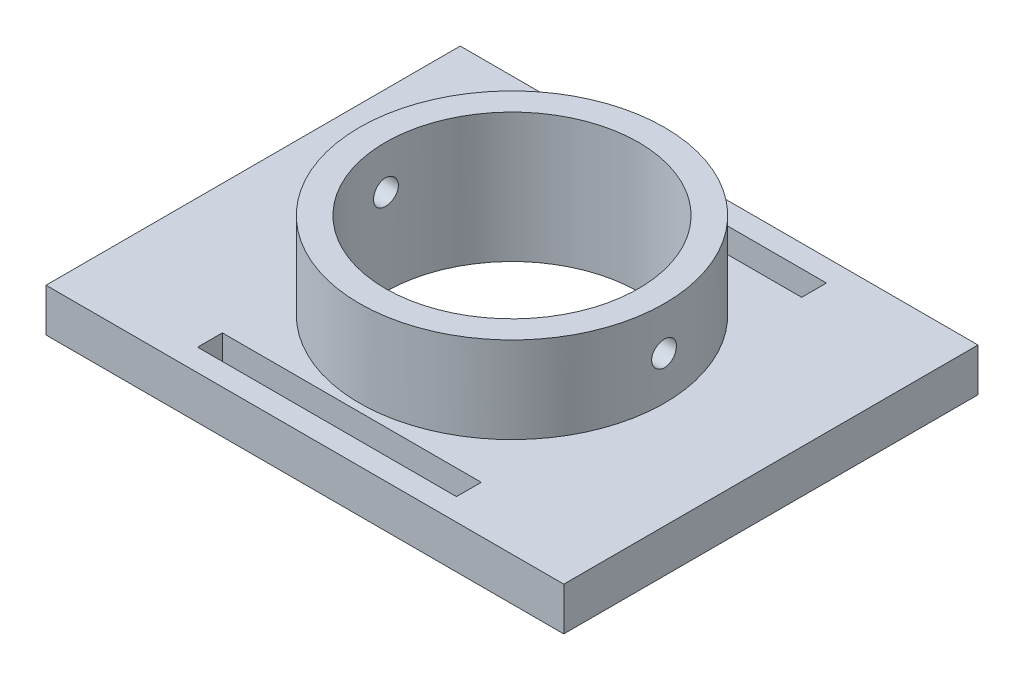
SolidWorks part; units mm, degrees
ref_plane "Alzado" through (0, 0, 0) normal (0, 0, 1) x (1, 0, 0)
ref_plane "Planta" through (0, 0, 0) normal (0, 1, 0) x (1, 0, 0)
ref_plane "Vista lateral" through (0, 0, 0) normal (1, 0, 0) x (0, 0, -1)
sketch "Croquis1" plane through (0, 0, 0) normal (0, 1, 0) x (1, 0, 0)
  line L1 (-30, 24) -> (30, 24)
  line L2 (-30, 24) -> (-30, -24)
  line L3 (-30, -24) -> (30, -24)
  line L4 (30, 24) -> (30, -24)
  line L5 (-30, 24) -> (30, -24) construction
  line L6 (-30, -24) -> (30, 24) construction
  point P0 (0, 0)
  dimension "D1" = 48
  dimension "D2" = 60
extrude "Saliente-Extruir1" add sketch "Croquis1" along normal blind 5 contours L2 L3 L4 L1
sketch "Croquis2" plane through (0, 5, 0) normal (0, 1, 0) x (1, 0, 0)
  circle A0 centre (0, 0) radius 17.675
  dimension "D1" = 35.35
extrude "Saliente-Extruir2" add sketch "Croquis2" along normal blind 10
sketch "Croquis3" plane through (0, 0, 0) normal (0, -1, 0) x (1, 0, 0)
  circle A0 centre (0, 0) radius 14.675
  dimension "D1" = 29.35
extrude "Cortar-Extruir1" cut sketch "Croquis3" against normal up to next
sketch "Croquis5" plane through (0, 5, 0) normal (0, 1, 0) x (1, 0, 0)
  line L1 (-15, 21.435) -> (15, 21.435)
  line L2 (-15, 21.435) -> (-15, 18.565)
  line L3 (-15, 18.565) -> (15, 18.565)
  line L4 (15, 21.435) -> (15, 18.565)
  line L5 (-15, 21.435) -> (15, 18.565) construction
  line L6 (-15, 18.565) -> (15, 21.435) construction
  line L7 (-15, -18.565) -> (15, -18.565)
  line L8 (-15, -18.565) -> (-15, -21.435)
  line L9 (-15, -21.435) -> (15, -21.435)
  line L10 (15, -18.565) -> (15, -21.435)
  line L11 (-15, -18.565) -> (15, -21.435) construction
  line L12 (-15, -21.435) -> (15, -18.565) construction
  point P0 (0, 20)
  point P5 (0, -20)
  point P13 (-4.3291, -9.4694)
  point P14 (-14.4489, 19.9563)
  dimension "D1" = 40
  dimension "D2" = 2.87
  dimension "D3" = 2.87
  dimension "D4" = 20
  dimension "D5" = 0
  dimension "D6" = 0
  dimension "D7" = 30
  dimension "D8" = 30
extrude "Cortar-Extruir2" cut sketch "Croquis5" against normal through all
sketch "Croquis6" plane through (0, 0, 0) normal (1, 0, 0) x (0, 0, -1)
  line L0 (17.675, 15) -> (-17.675, 15) construction
  circle A0 centre (0, 10) radius 1.435
  dimension "D1" = 2.87
  dimension "D2" = 5
extrude "Cortar-Extruir3" cut sketch "Croquis6" against normal through all both and the other way through all contours A0
